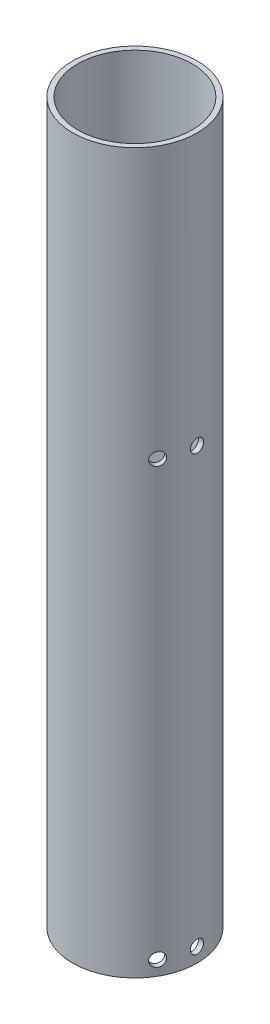
SolidWorks part; units mm, degrees
ref_plane "Front Plane" through (0, 0, 0) normal (0, 0, 1) x (1, 0, 0)
ref_plane "Top Plane" through (0, 0, 0) normal (0, 1, 0) x (1, 0, 0)
ref_plane "Right Plane" through (0, 0, 0) normal (1, 0, 0) x (0, 0, -1)
sketch "Sketch1" plane through (0, 0, 0) normal (0, 1, 0) x (1, 0, 0)
  circle A0 centre (0, 0) radius 26
  circle A1 centre (0, 0) radius 23.9
  dimension "D1" = 52
  dimension "D2" = 47.8
extrude "Boss-Extrude1" add sketch "Sketch1" along normal blind 300
sketch "Sketch3" plane through (0, 0, 0) normal (0, 0, 1) x (1, 0, 0)
  line L0 (0, 6) -> (0, 0)
  line L1 (0, 6) -> (0, 187)
  circle A0 centre (0, 6) radius 2.75
  circle A1 centre (0, 187) radius 2.75
  dimension "D2" = 5.5
  dimension "D3" = 5.5
  dimension "D1" = 6
  dimension "D4" = 181
extrude "Cut-Extrude2" cut sketch "Sketch3" against normal through all
pattern_circular "CirPattern1" count 3 over 360 about axis through (0, 300, 0) along (0, -1, 0) of "Cut-Extrude2"
sketch "Sketch5" plane through (0, 0, 0) normal (1, 0, 0) x (0, 0, -1)
  line L0 (0, 6) -> (0, 0)
  line L1 (0, 6) -> (0, 187)
  circle A0 centre (0, 187) radius 2.75
  circle A1 centre (0, 6) radius 2.75
  dimension "D2" = 5.5
  dimension "D1" = 6
  dimension "D4" = 5.5
  dimension "D3" = 181
extrude "Cut-Extrude3" cut sketch "Sketch5" against normal through all both and the other way through all
equation "\"TubeOutsideDiameter\"= 52"
equation "\"D1@Sketch1\"=\"TubeOutsideDiameter\""
equation "\"TubeInnerDiameter\"= 47.8"
equation "\"ReleaseMechanisumHeight\"=100"
equation "\"WireDiameter\"=3.38983"
equation "\"servoHoleDiameter\"= 2.8"
equation "\"CordDiameter\"= 5"
equation "\"MountingBoldDiameter\"=2.8"
equation "\"TubeMountingBoltDiameter\"= 5"
equation "\"D2@Sketch1\"=\"TubeInnerDiameter\""
equation "\"CardTubeOutsideDiameter\"= 54.2"
equation "\"CardTubeInsideDiameter\"= 50.4"
equation "\"D1@Sketch3\"=6"
equation "\"D2@Sketch3\"=\"TubeMountingBoltDiameter\"+0.5"
equation "\"D3@Sketch3\"=\"TubeMountingBoltDiameter\"+0.5"
equation "\"D2@Sketch5\"=\"TubeMountingBoltDiameter\"+0.5"
equation "\"D4@Sketch5\"=\"TubeMountingBoltDiameter\"+0.5"
